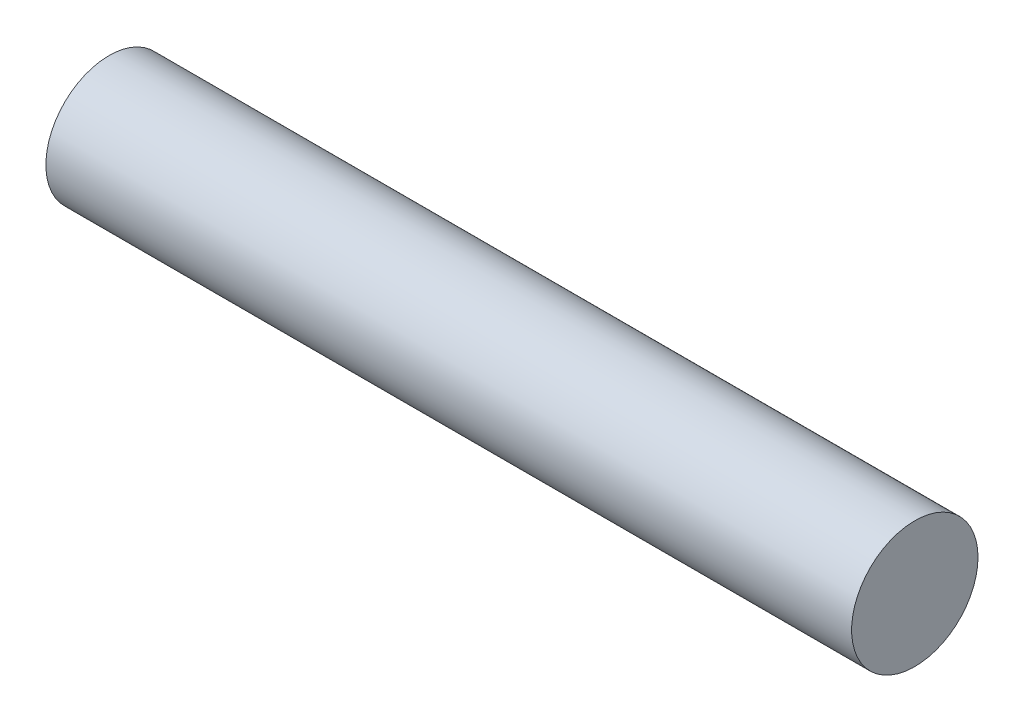
SolidWorks part; units mm, degrees
material "Plain Carbon Steel"
ref_plane "Front Plane" through (0, 0, 0) normal (0, 0, 1) x (1, 0, 0)
ref_plane "Top Plane" through (0, 0, 0) normal (0, 1, 0) x (1, 0, 0)
ref_plane "Right Plane" through (0, 0, 0) normal (1, 0, 0) x (0, 0, -1)
sketch "Sketch1" plane through (0, 0, 0) normal (1, 0, 0) x (0, 0, -1)
  circle A0 centre (0, 0) radius 6.35
extrude "Boss-Extrude1" add sketch "Sketch1" along normal blind 80.9625
